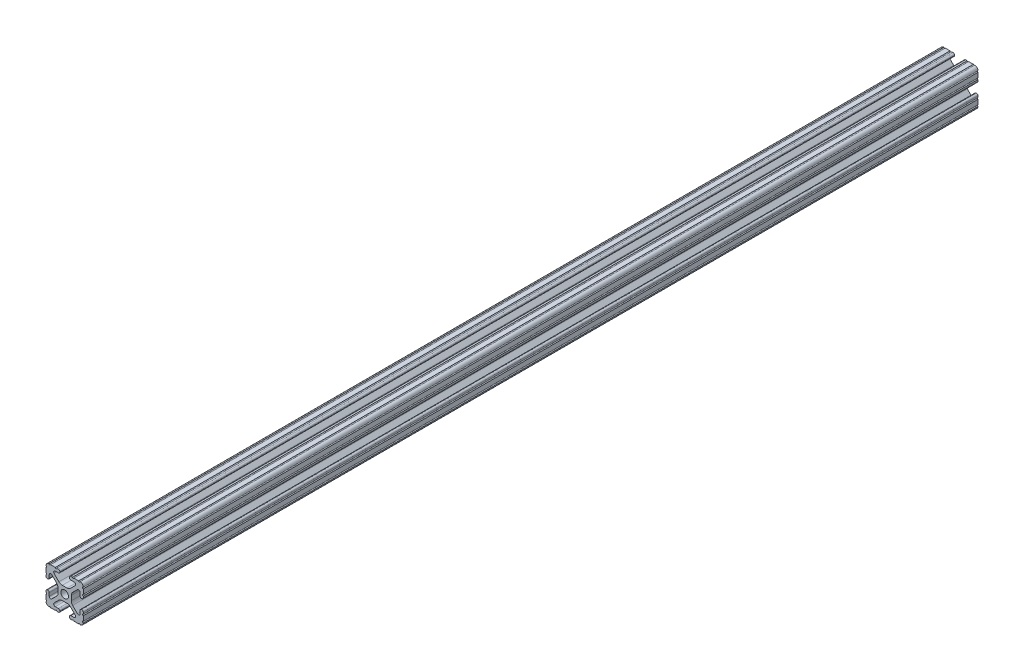
SolidWorks part; units mm, degrees
ref_plane "Front Plane" through (0, 0, 0) normal (0, 0, 1) x (1, 0, 0)
ref_plane "Top Plane" through (0, 0, 0) normal (0, 1, 0) x (1, 0, 0)
ref_plane "Right Plane" through (0, 0, 0) normal (1, 0, 0) x (0, 0, -1)
sketch "Sketch1" plane through (0, 0, 0) normal (0, 0, 1) x (1, 0, 0)
  line L88 (-7.1797, -8.6452) -> (-3.9523, -5.4237)
  line L89 (-1.7093, -4.4958) -> (1.7093, -4.4958)
  line L90 (3.9523, -5.4237) -> (7.1797, -8.6452)
  line L91 (6.4164, -10.4902) -> (4.2875, -10.4902)
  line L92 (3.2385, -11.5392) -> (3.2385, -11.651)
  line L93 (4.2875, -12.7) -> (5.3171, -12.7)
  line L94 (6.3331, -12.7) -> (9.5504, -12.7)
  line L95 (12.7, -9.5504) -> (12.7, -6.3331)
  line L96 (12.7, -5.3171) -> (12.7, -4.2875)
  line L97 (11.651, -3.2385) -> (11.5392, -3.2385)
  line L98 (10.4902, -4.2875) -> (10.4902, -6.4021)
  line L99 (8.7371, -7.1294) -> (5.441, -3.8408)
  line L100 (4.5085, -1.5932) -> (4.5085, 1.5932)
  line L101 (5.441, 3.8408) -> (8.7371, 7.1294)
  line L102 (10.4902, 6.4021) -> (10.4902, 4.2875)
  line L103 (11.5392, 3.2385) -> (11.651, 3.2385)
  line L104 (12.7, 4.2875) -> (12.7, 5.3171)
  line L105 (12.7, 6.3331) -> (12.7, 9.5504)
  line L106 (9.5504, 12.7) -> (6.3331, 12.7)
  line L107 (5.3171, 12.7) -> (4.2875, 12.7)
  line L108 (3.2385, 11.651) -> (3.2385, 11.5392)
  line L109 (4.2875, 10.4902) -> (6.4768, 10.4902)
  line L110 (7.207, 8.7244) -> (3.8983, 5.4232)
  line L111 (1.6558, 4.4958) -> (-1.6558, 4.4958)
  line L112 (-3.8983, 5.4232) -> (-7.207, 8.7244)
  line L113 (-6.4768, 10.4902) -> (-4.2875, 10.4902)
  line L114 (-3.2385, 11.5392) -> (-3.2385, 11.651)
  line L115 (-4.2875, 12.7) -> (-5.3171, 12.7)
  line L116 (-6.3331, 12.7) -> (-9.5504, 12.7)
  line L117 (-12.7, 9.5504) -> (-12.7, 6.3331)
  line L118 (-12.7, 5.3171) -> (-12.7, 4.2875)
  line L119 (-11.651, 3.2385) -> (-11.5392, 3.2385)
  line L120 (-10.4902, 4.2875) -> (-10.4902, 6.4021)
  line L121 (-8.7371, 7.1294) -> (-5.441, 3.8408)
  line L122 (-4.5085, 1.5932) -> (-4.5085, -1.5932)
  line L123 (-5.441, -3.8408) -> (-8.7371, -7.1294)
  line L124 (-10.4902, -6.4021) -> (-10.4902, -4.2875)
  line L125 (-11.5392, -3.2385) -> (-11.651, -3.2385)
  line L126 (-12.7, -4.2875) -> (-12.7, -5.3171)
  line L127 (-12.7, -6.3331) -> (-12.7, -9.5504)
  line L128 (-9.5504, -12.7) -> (-6.3331, -12.7)
  line L129 (-5.3171, -12.7) -> (-4.2875, -12.7)
  line L130 (-3.2385, -11.651) -> (-3.2385, -11.5392)
  line L131 (-4.2875, -10.4902) -> (-6.4164, -10.4902)
  circle A1 centre (0, 0) radius 2.6035
  arc A104 (-7.1797, -8.6452) -> (-6.4164, -10.4902) centre (-6.4164, -9.4098) ccw
  arc A105 (-1.7093, -4.4958) -> (-3.9523, -5.4237) centre (-1.7093, -7.6708) ccw
  arc A106 (3.9523, -5.4237) -> (1.7093, -4.4958) centre (1.7093, -7.6708) ccw
  arc A107 (6.4164, -10.4902) -> (7.1797, -8.6452) centre (6.4164, -9.4098) ccw
  arc A108 (4.2875, -10.4902) -> (3.2385, -11.5392) centre (4.2875, -11.5392) ccw
  arc A109 (3.2385, -11.651) -> (4.2875, -12.7) centre (4.2875, -11.651) ccw
  arc A110 (6.3331, -12.7) -> (5.3171, -12.7) centre (5.8251, -12.7) ccw
  arc A111 (10.5664, -12.6998) -> (9.5504, -12.7) centre (10.0584, -12.7) ccw
  arc A112 (10.5664, -12.6998) -> (12.6998, -10.5664) centre (10.5918, -10.5918) ccw
  arc A113 (12.7, -9.5504) -> (12.6998, -10.5664) centre (12.7, -10.0584) ccw
  arc A114 (12.7, -5.3171) -> (12.7, -6.3331) centre (12.7, -5.8251) ccw
  arc A115 (12.7, -4.2875) -> (11.651, -3.2385) centre (11.651, -4.2875) ccw
  arc A116 (11.5392, -3.2385) -> (10.4902, -4.2875) centre (11.5392, -4.2875) ccw
  arc A117 (8.7371, -7.1294) -> (10.4902, -6.4021) centre (9.4628, -6.4021) ccw
  arc A118 (4.5085, -1.5932) -> (5.441, -3.8408) centre (7.6835, -1.5932) ccw
  arc A119 (5.441, 3.8408) -> (4.5085, 1.5932) centre (7.6835, 1.5932) ccw
  arc A120 (10.4902, 6.4021) -> (8.7371, 7.1294) centre (9.4628, 6.4021) ccw
  arc A121 (10.4902, 4.2875) -> (11.5392, 3.2385) centre (11.5392, 4.2875) ccw
  arc A122 (11.651, 3.2385) -> (12.7, 4.2875) centre (11.651, 4.2875) ccw
  arc A123 (12.7, 6.3331) -> (12.7, 5.3171) centre (12.7, 5.8251) ccw
  arc A124 (12.6998, 10.5664) -> (12.7, 9.5504) centre (12.7, 10.0584) ccw
  arc A125 (12.6998, 10.5664) -> (10.5664, 12.6998) centre (10.5918, 10.5918) ccw
  arc A126 (9.5504, 12.7) -> (10.5664, 12.6998) centre (10.0584, 12.7) ccw
  arc A127 (5.3171, 12.7) -> (6.3331, 12.7) centre (5.8251, 12.7) ccw
  arc A128 (4.2875, 12.7) -> (3.2385, 11.651) centre (4.2875, 11.651) ccw
  arc A129 (3.2385, 11.5392) -> (4.2875, 10.4902) centre (4.2875, 11.5392) ccw
  arc A130 (7.207, 8.7244) -> (6.4768, 10.4902) centre (6.4768, 9.4563) ccw
  arc A131 (1.6558, 4.4958) -> (3.8983, 5.4232) centre (1.6558, 7.6708) ccw
  arc A132 (-3.8983, 5.4232) -> (-1.6558, 4.4958) centre (-1.6558, 7.6708) ccw
  arc A133 (-6.4768, 10.4902) -> (-7.207, 8.7244) centre (-6.4768, 9.4563) ccw
  arc A134 (-4.2875, 10.4902) -> (-3.2385, 11.5392) centre (-4.2875, 11.5392) ccw
  arc A135 (-3.2385, 11.651) -> (-4.2875, 12.7) centre (-4.2875, 11.651) ccw
  arc A136 (-6.3331, 12.7) -> (-5.3171, 12.7) centre (-5.8251, 12.7) ccw
  arc A137 (-10.5664, 12.6998) -> (-9.5504, 12.7) centre (-10.0584, 12.7) ccw
  arc A138 (-10.5664, 12.6998) -> (-12.6998, 10.5664) centre (-10.5918, 10.5918) ccw
  arc A139 (-12.7, 9.5504) -> (-12.6998, 10.5664) centre (-12.7, 10.0584) ccw
  arc A140 (-12.7, 5.3171) -> (-12.7, 6.3331) centre (-12.7, 5.8251) ccw
  arc A141 (-12.7, 4.2875) -> (-11.651, 3.2385) centre (-11.651, 4.2875) ccw
  arc A142 (-11.5392, 3.2385) -> (-10.4902, 4.2875) centre (-11.5392, 4.2875) ccw
  arc A143 (-8.7371, 7.1294) -> (-10.4902, 6.4021) centre (-9.4628, 6.4021) ccw
  arc A144 (-4.5085, 1.5932) -> (-5.441, 3.8408) centre (-7.6835, 1.5932) ccw
  arc A145 (-5.441, -3.8408) -> (-4.5085, -1.5932) centre (-7.6835, -1.5932) ccw
  arc A146 (-10.4902, -6.4021) -> (-8.7371, -7.1294) centre (-9.4628, -6.4021) ccw
  arc A147 (-10.4902, -4.2875) -> (-11.5392, -3.2385) centre (-11.5392, -4.2875) ccw
  arc A148 (-11.651, -3.2385) -> (-12.7, -4.2875) centre (-11.651, -4.2875) ccw
  arc A149 (-12.7, -6.3331) -> (-12.7, -5.3171) centre (-12.7, -5.8251) ccw
  arc A150 (-12.6998, -10.5664) -> (-12.7, -9.5504) centre (-12.7, -10.0584) ccw
  arc A151 (-12.6998, -10.5664) -> (-10.5664, -12.6998) centre (-10.5918, -10.5918) ccw
  arc A152 (-9.5504, -12.7) -> (-10.5664, -12.6998) centre (-10.0584, -12.7) ccw
  arc A153 (-5.3171, -12.7) -> (-6.3331, -12.7) centre (-5.8251, -12.7) ccw
  arc A154 (-4.2875, -12.7) -> (-3.2385, -11.651) centre (-4.2875, -11.651) ccw
  arc A155 (-3.2385, -11.5392) -> (-4.2875, -10.4902) centre (-4.2875, -11.5392) ccw
extrude "Boss-Extrude1" add sketch "Sketch1" along normal mid plane 609.6
